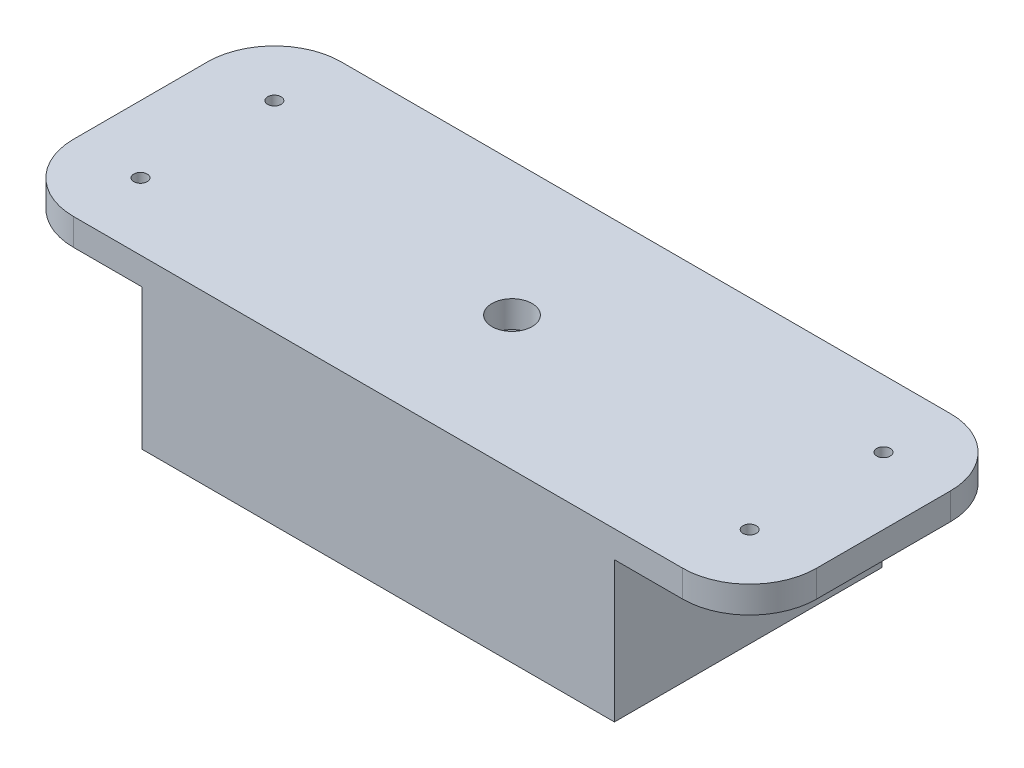
SolidWorks part; units mm, degrees
ref_plane "Front Plane" through (0, 0, 0) normal (0, 0, 1) x (1, 0, 0)
ref_plane "Top Plane" through (0, 0, 0) normal (0, 1, 0) x (1, 0, 0)
ref_plane "Right Plane" through (0, 0, 0) normal (1, 0, 0) x (0, 0, -1)
sketch "Sketch1" plane through (0, 0, 0) normal (0, 1, 0) x (1, 0, 0)
  line L0 (-35.5, 0) -> (-35.5, -20)
  line L1 (-45.5, 20) -> (45.5, 20)
  line L2 (-55.5, 10) -> (-55.5, -10)
  line L3 (-45.5, -20) -> (45.5, -20)
  line L4 (55.5, 10) -> (55.5, -10)
  line L5 (-35.5, 43.0018) -> (-55.5, 43.0018)
  line L6 (-35.5, 20) -> (-35.5, 0)
  line L8 (-55.5, 10) -> (-55.5, 0)
  circle A1 centre (0, 0) radius 1
  arc A2 (45.5, -20) -> (55.5, -10) centre (45.5, -10) ccw
  arc A3 (-55.5, -10) -> (-45.5, -20) centre (-45.5, -10) ccw
  arc A4 (45.5, 20) -> (55.5, 10) centre (45.5, 10) cw
  arc A5 (-45.5, 20) -> (-55.5, 10) centre (-45.5, 10) ccw
  circle A6 centre (-45.5, 10) radius 1
  circle A7 centre (-45.5, -10) radius 1
  circle A8 centre (45.5, 10) radius 1
  circle A9 centre (45.5, -10) radius 1
  point P0 (0, 0)
  point P6 (25.5, 0)
  point P7 (-25.5, 0)
  point P10 (55.5, -20)
  point P15 (55.5, 20)
  dimension "D2" = 2
  dimension "D3" = 10
  dimension "D4" = 2
  dimension "D1" = 40
extrude "Boss-Extrude1" add sketch "Sketch1" along normal blind 4 contours A4 L1 L6 L0 L3 A2 L4 A9 A8 A1 | L1 A5 L2 A3 L3 L0 L6 A7 A6
sketch "Sketch2" plane through (0, 4, 0) normal (0, 1, 0) x (1, 0, 0)
  line L0 (-35.5, -20) -> (35.3, -20)
  line L1 (-35.3, 20) -> (35.3, 20)
  line L3 (-35.5, -20) -> (-35.3, -20)
  line L5 (35.3, 0) -> (35.3, -20)
  line L6 (35.3, 20) -> (35.3, 0)
  line L7 (-35.3, 20) -> (-35.3, 0)
  line L8 (-35.3, 0) -> (-35.3, -20)
  line L9 (-33.8, -18.5) -> (33.8, -18.5)
  line L10 (33.8, 0) -> (33.8, -18.5)
  line L11 (33.8, 18.5) -> (33.8, 0)
  line L12 (-33.8, 18.5) -> (33.8, 18.5)
  line L13 (-33.8, 18.5) -> (-33.8, 0)
  line L14 (-33.8, 0) -> (-33.8, -18.5)
  line L15 (-33.8, -18.5) -> (-33.8, -18.5)
  arc A11 (-45.5, 20) -> (-55.5, 10) centre (-45.5, 10) ccw construction
  point P4 (0, 0)
  point P10 (25.5, 0)
  point P11 (-25.5, 0)
  point P30 (-52.5711, 17.0711)
  point P31 (-52.5711, 17.0711)
  line M4 (45.5, 20) -> (-45.5, 20)
  dimension "D1" = 1.5
extrude "Boss-Extrude3" add sketch "Sketch2" against normal blind 25 contours L7 L8 L0 L5 L6 L14 L13 L12 L11 L10 L9 M4
sketch "Sketch3" plane through (0, 4, 0) normal (0, 1, 0) x (1, 0, 0)
  circle A1 centre (0, 0) radius 3
  dimension "D1" = 6
extrude "Cut-Extrude1" cut sketch "Sketch3" against normal blind 20
